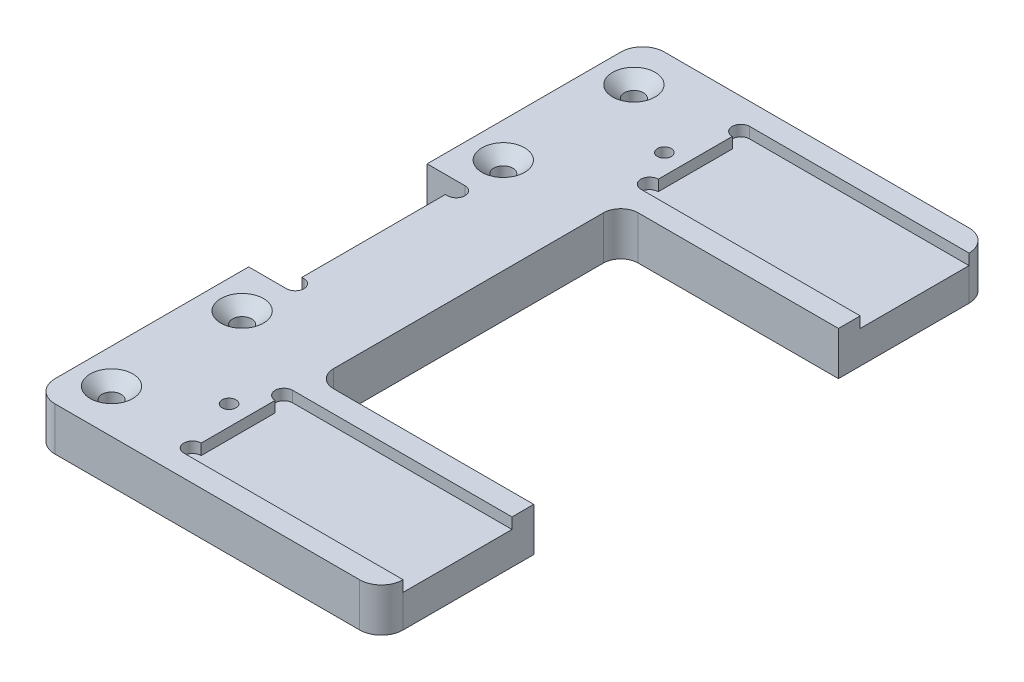
SolidWorks part; units mm, degrees
material "7075-T6 (SN)"
ref_plane "Front Plane" through (0, 0, 0) normal (0, 0, 1) x (1, 0, 0)
ref_plane "Top Plane" through (0, 0, 0) normal (0, 1, 0) x (1, 0, 0)
ref_plane "Right Plane" through (0, 0, 0) normal (1, 0, 0) x (0, 0, -1)
sketch "Sketch1" plane through (0, 0, 0) normal (0, 1, 0) x (1, 0, 0)
  line L0 (0, 35) -> (0, 10.25)
  line L1 (0, 10.25) -> (4.1, 10.25)
  line L2 (4.1, 10.25) -> (4.1, -10.25)
  line L3 (4.1, -10.25) -> (0, -10.25)
  line L4 (0, -10.25) -> (0, -35)
  line L5 (0, -35) -> (40, -35)
  line L6 (40, -35) -> (40, -17.5)
  line L7 (40, -17.5) -> (15, -17.5)
  line L8 (15, -17.5) -> (15, 17.5)
  line L9 (15, 17.5) -> (40, 17.5)
  line L10 (40, 17.5) -> (40, 35)
  line L11 (40, 35) -> (0, 35)
  point P0 (4.1, 0)
  point P15 (15, 0)
  dimension "D1" = 4.1
  dimension "D2" = 70
  dimension "D3" = 20.5
  dimension "D4" = 25
  dimension "D5" = 15
  dimension "D6" = 17.5
extrude "Boss-Extrude1" add sketch "Sketch1" along normal blind 5
fillet "Fillet1" radius 2 2 edges at (15, 2.5, 17.5) (15, 2.5, -17.5)
fillet "Fillet2" radius 2.5 4 edges at (0, 2.5, -35) (0, 2.5, 35) (40, 2.5, -35) (40, 2.5, 35)
sketch "Sketch3" plane through (0, 5, 0) normal (0, 1, 0) x (1, 0, 0)
  line L0 (4.1, 10.25) -> (4.35, 10.25)
  line L1 (4.35, 8.25) -> (4.1, 8.25)
  line L2 (4.1, 10.25) -> (4.1, -10.25) construction
  line L3 (4.1, 8.25) -> (4.1, 10.25)
  line L4 (4.1, -10.25) -> (4.1, -8.25)
  line L5 (4.1, -8.25) -> (4.35, -8.25)
  line L6 (4.35, -10.25) -> (4.1, -10.25)
  arc A0 (4.35, 10.25) -> (4.35, 8.25) centre (4.35, 9.25) cw
  arc A1 (4.35, -8.25) -> (4.35, -10.25) centre (4.35, -9.25) cw
  dimension "D1" = 1
  dimension "D2" = 0.25
extrude "Cut-Extrude2" cut sketch "Sketch3" against normal up to next
hole_wizard "CSK for M2 Countersunk Flat Head Screw1" positions "Sketch4" profile "Sketch5" countersink size "M2" standard "DIN" end condition up to next
sketch "Sketch4" plane through (0, 5, 0) normal (0, 1, 0) x (1, 0, 0)
  line L0 (2.5, -35) -> (37.5, -35) construction
  line L1 (37.5, 35) -> (2.5, 35) construction
  line L2 (0, 32.5) -> (0, 10.25) construction
  point P0 (4, 30)
  point P2 (4, 15)
  point P4 (4, -15)
  point P6 (4, -30)
  dimension "D1" = 5
  dimension "D2" = 15
  dimension "D3" = 15
  dimension "D4" = 5
  dimension "D5" = 4
sketch "Sketch5" plane through (4, 5, -30) normal (1, 0, 0) x (0, 0, 1)
  line L0 (0, 0) -> (0, 5)
  line L1 (0, 5) -> (1.1, 5)
  line L2 (1.1, 5) -> (1.1, 1.35)
  line L3 (1.1, 1.35) -> (2.45, 0)
  line L5 (2.45, 0) -> (0, 0)
  line L6 (-1.1, 1.35) -> (-2.45, 0) construction
  line L11 (0, -6.35) -> (0, 107.95) construction
  dimension "Thru Hole Dia." = 2.2
  dimension "Thru Hole Depth" = 5
  dimension "Near C'Sink Dia." = 4.9
  dimension "Near C'Sink Angle" = 90
hole_wizard "M2 Tapped Hole1" positions "Sketch6" profile "Sketch8" tap size "M2" standard "DIN" end condition up to next
sketch "Sketch6" plane through (0, 5, 0) normal (0, 1, 0) x (1, 0, 0)
  line L0 (0, 32.5) -> (0, 10.25) construction
  line L1 (37.5, 35) -> (2.5, 35) construction
  line L2 (2.5, -35) -> (37.5, -35) construction
  point P0 (12.5, -25)
  point P2 (12.5, 25)
  dimension "D1" = 12.5
  dimension "D2" = 10
  dimension "D3" = 10
sketch "Sketch8" plane through (12.5, 5, 25) normal (1, 0, 0) x (0, 0, 1)
  line L0 (0, 0) -> (0, 5)
  line L1 (0, 5) -> (0.8, 5)
  line L2 (0.8, 5) -> (0.8, 0)
  line L5 (0.8, 0) -> (0, 0)
  line L11 (0, -6.35) -> (0, 107.95) construction
  dimension "Thru Tap Drill Dia." = 1.6
  dimension "Thru Tap Drill Depth" = 5
cosmetic thread "Hole Thread1" parameters "D2"=2
cosmetic thread "Hole Thread2" parameters "D2"=2
sketch "Sketch9" plane through (0, 5, 0) normal (0, 1, 0) x (1, 0, 0)
  line L7 (40, 17.5) -> (40, 32.5) construction
  line L8 (14.8, 32.5) -> (40, 32.5)
  line L9 (14.8, 32.5) -> (14.8, 20)
  line L10 (14.8, 20) -> (40, 20)
  line L11 (40, 32.5) -> (40, 20)
  line L15 (40, -32.5) -> (14.8, -32.5)
  line L16 (40, -32.5) -> (40, -20)
  line L17 (40, -20) -> (14.8, -20)
  line L18 (14.8, -32.5) -> (14.8, -20)
  dimension "D1" = 12.5
  dimension "D2" = 25.2
extrude "Cut-Extrude3" cut sketch "Sketch9" against normal blind 1.25
sketch "Sketch10" plane through (0, 5, 0) normal (0, 1, 0) x (1, 0, 0)
  line L0 (14.8, 32.5) -> (14.8, 20) construction
  line L1 (14.8, 32.5) -> (14.8, 20) construction
  line L2 (14.8, 22) -> (14.8, 20)
  line L3 (14.8, 30.5) -> (14.8, 32.5)
  arc A0 (14.8, 32.5) -> (14.8, 30.5) centre (14.8, 31.5) ccw
  arc A1 (14.8, 20) -> (14.8, 22) centre (14.8, 21) cw
  dimension "D1" = 2
extrude "Cut-Extrude4" cut sketch "Sketch10" against normal up to surface (1.25 mm away) up to face at (27.4, 3.75, -26.25)
ref_plane "Plane1" through (0, 2.5, 0) normal (0, -1, 0) x (-1, 0, 0)
mirror "Mirror1" about plane through (0, 2.5, 0) normal (0, -1, 0) of "CSK for M2 Countersunk Flat Head Screw1"
mirror "Mirror2" about plane through (0, 0, 0) normal (0, 0, 1) of "Cut-Extrude4"
